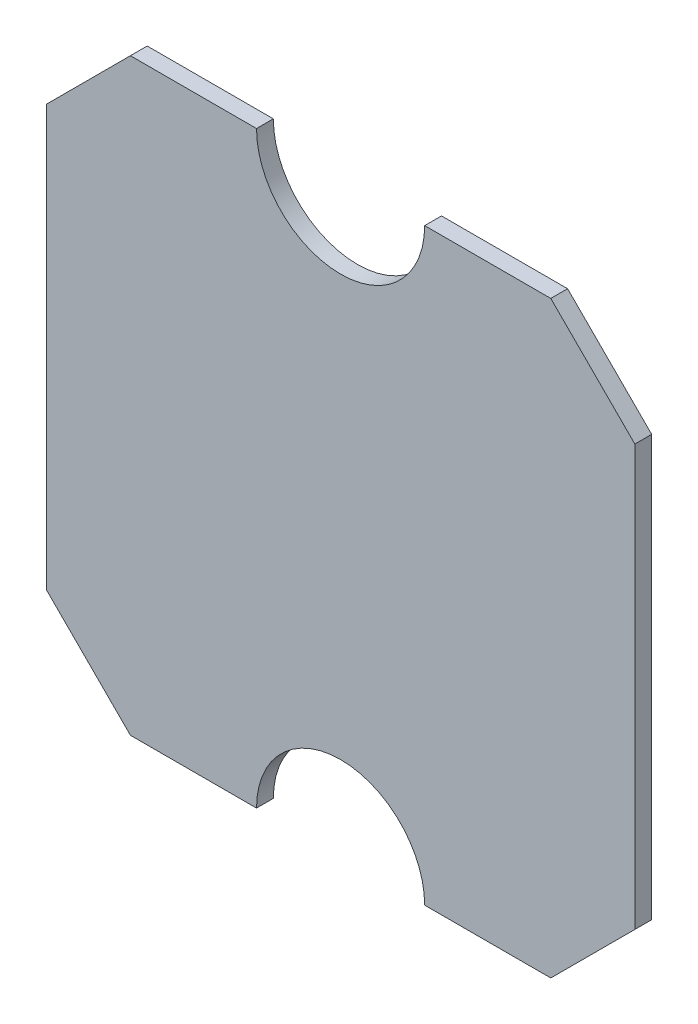
SolidWorks part; units mm, degrees
ref_plane "Front Plane" through (0, 0, 0) normal (0, 0, 1) x (1, 0, 0)
ref_plane "Top Plane" through (0, 0, 0) normal (0, 1, 0) x (1, 0, 0)
ref_plane "Right Plane" through (0, 0, 0) normal (1, 0, 0) x (0, 0, -1)
sketch "Sketch1" plane through (0, 0, 0) normal (0, 0, 1) x (1, 0, 0)
  line L0 (-175, 0) -> (175, 0) construction
  line L1 (175, 125) -> (175, -125)
  line L2 (0, 0) -> (0, 125) construction
  line L3 (175, 125) -> (125, 175)
  line L4 (125, 175) -> (50, 175)
  line L5 (-175, 125) -> (-175, -125)
  line L6 (-175, 125) -> (-125, 175)
  line L7 (-125, 175) -> (-50, 175)
  line L8 (175, -125) -> (125, -175)
  line L9 (125, -175) -> (50, -175)
  line L10 (-125, -175) -> (-50, -175)
  line L11 (-175, -125) -> (-125, -175)
  arc A0 (50, 175) -> (-50, 175) centre (0, 175) cw
  arc A1 (50, -175) -> (-50, -175) centre (0, -175) ccw
  point P2 (0, 0)
  point P8 (175, 0)
  point P13 (0, 0)
  point P14 (0, 0)
  point P15 (0, 125)
  dimension "D5" = 50
  dimension "D1" = 350
  dimension "D2" = 350
  dimension "D3" = 50
  dimension "D4" = 50
extrude "Boss-Extrude1" add sketch "Sketch1" along normal mid plane 10
